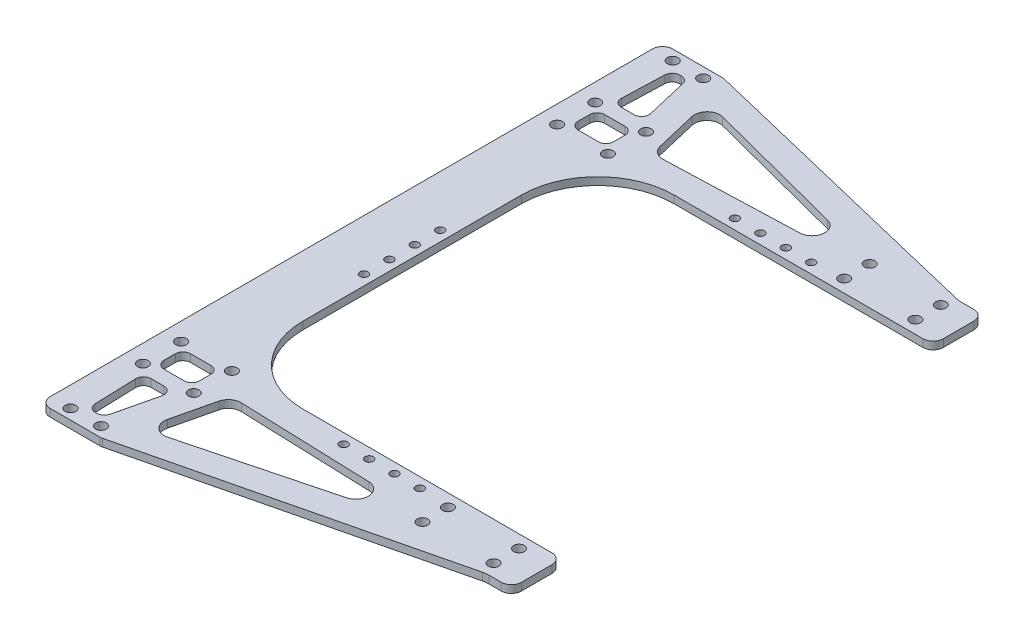
SolidWorks part; units mm, degrees
material "Thornel Mat VMA"
ref_plane "前视基准面" through (0, 0, 0) normal (0, 0, 1) x (1, 0, 0)
ref_plane "上视基准面" through (0, 0, 0) normal (0, 1, 0) x (1, 0, 0)
ref_plane "右视基准面" through (0, 0, 0) normal (1, 0, 0) x (0, 0, -1)
sketch "草图1" plane through (0, 0, 0) normal (0, 1, 0) x (1, 0, 0)
  line L0 (0, -83) -> (0, 83) construction
  line L5 (0, 0) -> (71.3718, 0) construction
  line L6 (14, 88) -> (-14, 88) construction
  line L7 (14, 88) -> (14, 78) construction
  line L8 (14, 78) -> (-14, 78) construction
  line L9 (-14, 88) -> (-14, 78) construction
  line L10 (14, 88) -> (-14, 78) construction
  line L11 (14, 78) -> (-14, 88) construction
  line L12 (14, -88) -> (-14, -88) construction
  line L13 (14, -88) -> (14, -78) construction
  line L14 (14, -78) -> (-14, -78) construction
  line L15 (-14, -88) -> (-14, -78) construction
  line L16 (14, -88) -> (-14, -78) construction
  line L17 (14, -78) -> (-14, -88) construction
  line L18 (-26, 93) -> (-96, 93)
  line L19 (26, 93) -> (-26, 93)
  line L20 (26, 93) -> (26, 73)
  line L21 (26, 73) -> (-26, 73) construction
  line L22 (-26, 93) -> (-26, 73) construction
  line L23 (26, 93) -> (-26, 73) construction
  line L24 (26, 73) -> (-26, 93) construction
  line L25 (-106, 103) -> (-106, 122.5)
  line L26 (-106, 122.5) -> (-130, 122.5)
  line L27 (-26, 73) -> (-76, 73) construction
  line L28 (-106, 43) -> (-106, -43)
  line L29 (26, -93) -> (26, -73)
  line L30 (26, -73) -> (-26, -73) construction
  line L31 (26, -93) -> (-26, -93)
  line L32 (-26, -93) -> (-96, -93)
  line L33 (-26, -73) -> (-76, -73) construction
  line L34 (-106, -103) -> (-106, -122.5)
  line L35 (-106, -122.5) -> (-130, -122.5)
  line L36 (-130, 122.5) -> (-130, -122.5)
  line L37 (-76, -73) -> (26, -73)
  line L38 (-76, 73) -> (26, 73)
  circle A0 centre (-14, 88) radius 2.1
  circle A1 centre (-14, 78) radius 2.1
  circle A4 centre (14, 78) radius 2.1
  circle A5 centre (14, 88) radius 2.1
  arc A6 (-96, 93) -> (-106, 103) centre (-96, 103) cw
  arc A7 (-76, 73) -> (-106, 43) centre (-76, 43) ccw
  circle A8 centre (14, -78) radius 2.1
  circle A9 centre (14, -88) radius 2.1
  circle A12 centre (-14, -78) radius 2.1
  circle A13 centre (-14, -88) radius 2.1
  arc A14 (-76, -73) -> (-106, -43) centre (-76, -43) cw
  arc A15 (-96, -93) -> (-106, -103) centre (-96, -103) ccw
  point P3 (0, 0)
  dimension "D4" = 4.2
  dimension "D8" = 10
  dimension "D11" = 30
  dimension "D1" = 166
  dimension "D2" = 10
  dimension "D3" = 28
  dimension "D5" = 20
  dimension "D6" = 52
  dimension "D7" = 106
  dimension "D9" = 24
  dimension "D10" = 245
extrude "凸台-拉伸1" add sketch "草图1" along normal blind 3
fillet "圆角1" radius 4 4 edges at (-130, 1.5, 122.5) (-130, 1.5, -122.5) (26, 1.5, 73) (26, 1.5, -73)
sketch "草图2" plane through (0, 3, 0) normal (0, 1, 0) x (1, 0, 0)
  line L0 (-116, 122.5) -> (-116, -122.5) construction
  line L1 (-106, 122.5) -> (-126, 122.5) construction
  line L2 (-126, -122.5) -> (-106, -122.5) construction
  line L4 (-110, -118.5) -> (-122, -118.5) construction
  line L5 (-110, -118.5) -> (-110, 118.5) construction
  line L6 (-110, 118.5) -> (-122, 118.5) construction
  line L7 (-122, -118.5) -> (-122, 118.5) construction
  line L8 (-110, -118.5) -> (-122, 118.5) construction
  line L9 (-110, 118.5) -> (-122, -118.5) construction
  circle A0 centre (-122, 118.5) radius 2.1
  circle A1 centre (-110, 118.5) radius 2.1
  circle A2 centre (-122, -118.5) radius 2.1
  circle A3 centre (-110, -118.5) radius 2.1
  point P6 (-116, 0)
  dimension "D3" = 4.2
  dimension "D1" = 12
  dimension "D2" = 4
extrude "切除-拉伸1" cut sketch "草图2" against normal through all
sketch "草图4" plane through (0, 3, 0) normal (0, 1, 0) x (1, 0, 0)
  line L0 (-106, 122.5) -> (16, 93)
  line L2 (16, 93) -> (-106, 93)
  line L3 (-106, 93) -> (-106, 122.5)
  line L5 (0, 0) -> (-106, 0) construction
  line L6 (-106, -43) -> (-106, 43) construction
  line L7 (16, -93) -> (-106, -93)
  line L8 (-106, -122.5) -> (16, -93)
  line L9 (-106, -93) -> (-106, -122.5)
  line L11 (26, 93) -> (-96, 93) construction
  line L12 (26, 77) -> (26, 93) construction
  dimension "D1" = 10
extrude "凸台-拉伸2" add sketch "草图4" against normal up to surface (3 mm away) up to face at (-110, 0, -116.4)
fillet "圆角2" radius 4 4 edges at (-106, 1.5, 122.5) (-106, 1.5, -122.5) (26, 1.5, 93) (26, 1.5, -93)
sketch "草图5" plane through (0, 0, 0) normal (0, -1, 0) x (1, 0, 0)
  line L0 (-130, 0) -> (115.8212, 0) construction
  line L1 (-130, -118.5) -> (-130, 118.5) construction
  line L2 (-110, 98.3119) -> (-110, -42.0796) construction
  line L4 (-106, 43) -> (-106, -43) construction
  line L5 (-20.7358, -77) -> (-173.6293, -77) construction
  line L6 (-76, -73) -> (22, -73) construction
  line L7 (-20.7358, 77) -> (-173.6293, 77) construction
  line L8 (-26, -77) -> (-36, -77) construction
  circle A0 centre (-110, -15) radius 1.6
  circle A1 centre (-110, -5) radius 1.6
  circle A2 centre (-110, 5) radius 1.6
  circle A3 centre (-110, 15) radius 1.6
  circle A4 centre (-110, -15) radius 2.84 construction
  circle A5 centre (-26, -77) radius 1.6
  circle A6 centre (-36, -77) radius 1.6
  circle A7 centre (-46, -77) radius 1.6
  circle A8 centre (-56, -77) radius 1.6
  circle A9 centre (-26, -77) radius 2.84 construction
  circle A10 centre (-14, -78) radius 3.61 construction
  circle A11 centre (-56, 77) radius 1.6
  circle A12 centre (-46, 77) radius 1.6
  circle A13 centre (-36, 77) radius 1.6
  circle A14 centre (-26, 77) radius 1.6
  dimension "D1" = 3.2
  dimension "D4" = 5.68
  dimension "D9" = 7.22
  dimension "D10" = 5.68
  dimension "D2" = 10
  dimension "D3" = 5
  dimension "D5" = 4
  dimension "D7" = 10
  dimension "D8" = 4
  dimension "D11" = 12
  dimension "D6" = 4
extrude "切除-拉伸2" cut sketch "草图5" against normal through all
fillet "圆角3" radius 10 2 edges at (16, 1.5, 93) (16, 1.5, -93)
sketch "草图6" plane through (0, 3, 0) normal (0, 1, 0) x (1, 0, 0)
  circle A0 centre (-110, 118.5) radius 2.1 construction
  circle A1 centre (-122, 118.5) radius 2.1 construction
  circle A2 centre (-110, -118.5) radius 2.1 construction
  circle A3 centre (-122, -118.5) radius 2.1 construction
  circle A4 centre (-110, 118.5) radius 2.1
  circle A5 centre (-122, 118.5) radius 2.1
  circle A6 centre (-110, -118.5) radius 2.1
  circle A7 centre (-122, -118.5) radius 2.1
extrude "凸台-拉伸3" [suppressed] add sketch "草图6" against normal up to surface (3 mm away)
sketch "草图7" plane through (0, 3, 0) normal (0, 1, 0) x (1, 0, 0)
  line L0 (-130, 0) -> (-50130, 0) construction
  line L1 (-130, 118.5) -> (-130, -118.5) construction
  line L3 (-123, -74) -> (-103, -74) construction
  line L4 (-123, -74) -> (-123, -89) construction
  line L5 (-123, -89) -> (-103, -89) construction
  line L6 (-103, -74) -> (-103, -89) construction
  line L7 (-113, -89) -> (-113, -74) construction
  line L8 (-123, -81.5) -> (-103, -81.5) construction
  line L9 (-130, 118.5) -> (-130, -118.5) construction
  line L10 (-123, 81.5) -> (-103, 81.5) construction
  line L11 (-113, 89) -> (-113, 74) construction
  line L12 (-103, 74) -> (-103, 89) construction
  line L13 (-123, 89) -> (-103, 89) construction
  line L14 (-123, 74) -> (-123, 89) construction
  line L15 (-123, 74) -> (-103, 74) construction
  line L16 (-126, -122.5) -> (-106.4767, -122.5) construction
  line L17 (-14, -78) -> (14, -78) construction
  line L18 (-14, -78) -> (-14, -88) construction
  line L19 (-14, -88) -> (14, -88) construction
  line L20 (14, -78) -> (14, -88) construction
  line L21 (0, -88) -> (0, -78) construction
  line L22 (-14, -83) -> (14, -83) construction
  circle A0 centre (-123, -74) radius 2.1
  circle A1 centre (-103, -74) radius 2.1
  circle A3 centre (-103, -89) radius 2.1
  circle A4 centre (-123, -89) radius 2.1
  circle A5 centre (-123, 89) radius 2.1
  circle A6 centre (-103, 89) radius 2.1
  circle A7 centre (-103, 74) radius 2.1
  circle A8 centre (-123, 74) radius 2.1
  point P4 (-130, 0)
  point P5 (-113, -81.5)
  point P29 (-113, 81.5)
  point P108 (0, -83)
  dimension "D3" = 4.2
  dimension "D1" = 20
  dimension "D2" = 15
  dimension "D4" = 41
  dimension "D5" = 17
extrude "切除-拉伸3" cut sketch "草图7" against normal through all
sketch "草图8" plane through (0, 3, 0) normal (0, 1, 0) x (1, 0, 0)
  line L0 (0, 0) -> (-197.4028, 0) construction
  line L9 (26, 77) -> (26, 89) construction
  line L10 (-99.1731, 103.1913) -> (-95.2909, 86.8306)
  line L15 (-118, 62.5) -> (-121, 62.5) construction
  line L16 (-124, 59.5) -> (-124, -59.5) construction
  line L17 (-121, -62.5) -> (-118, -62.5) construction
  line L18 (-115, -59.5) -> (-115, 59.5) construction
  line L19 (-130, 118.5) -> (-130, -118.5) construction
  line L23 (-103, 89) -> (-123, 89) construction
  line L24 (-123, 89) -> (-123, 74) construction
  line L25 (-123, 74) -> (-103, 74) construction
  line L26 (-103, 74) -> (-103, 89) construction
  line L27 (-103, 89) -> (-123, 74) construction
  line L28 (-109, 86.75) -> (-117, 86.75)
  line L29 (-106, 83.75) -> (-106, 79.25)
  line L30 (-109, 76.25) -> (-117, 76.25)
  line L31 (-120, 83.75) -> (-120, 79.25)
  line L32 (-103, 74) -> (-123, 89) construction
  line L33 (-109, -76.25) -> (-117, -76.25)
  line L34 (-120, -83.75) -> (-120, -79.25)
  line L35 (-109, -86.75) -> (-117, -86.75)
  line L36 (-106, -83.75) -> (-106, -79.25)
  line L37 (-110, 118.5) -> (-103, 89) construction
  line L38 (-110, 118.5) -> (-122, 118.5) construction
  line L39 (-122, 118.5) -> (-123, 89) construction
  line L44 (-115.1381, 115) -> (-115.7166, 115)
  line L45 (-118.7149, 112.1016) -> (-119.2742, 95.6016)
  line L46 (-111.2229, 92.5) -> (-116.2759, 92.5)
  line L47 (-112.2192, 112.6926) -> (-108.3039, 96.1926)
  line L48 (-107.4277, 92.5) -> (-119.3793, 92.5) construction
  line L49 (-112.7667, 115) -> (-107.4277, 92.5) construction
  line L50 (-118.6166, 115) -> (-119.3793, 92.5) construction
  line L51 (-112.7667, 115) -> (-118.6166, 115) construction
  line L52 (-37.1814, 94.639) -> (-93.0484, 109.1844)
  line L53 (-38.2667, 84.8034) -> (-90.2514, 82.988)
  line L54 (-4, 86) -> (-66.1315, 86) construction
  line L55 (-4, 86) -> (-51.4736, 97.4793) construction
  line L56 (14.8415, 93.2801) -> (-105.5366, 122.388) construction
  line L57 (-76, 73) -> (22, 73) construction
  line L58 (-37.1814, -94.639) -> (-93.0484, -109.1844)
  line L59 (-38.2667, -84.8034) -> (-90.2514, -82.988)
  line L60 (-99.1731, -103.1913) -> (-95.2909, -86.8306)
  line L61 (-112.2192, -112.6926) -> (-108.3039, -96.1926)
  line L62 (-111.2229, -92.5) -> (-116.2759, -92.5)
  line L63 (-118.7149, -112.1016) -> (-119.2742, -95.6016)
  line L64 (-115.1381, -115) -> (-115.7166, -115)
  arc A0 (-37.1814, 94.639) -> (-38.2667, 84.8034) centre (-38.4412, 89.8003) cw
  arc A10 (-118, -62.5) -> (-115, -59.5) centre (-118, -59.5) ccw construction
  arc A11 (-124, -59.5) -> (-121, -62.5) centre (-121, -59.5) ccw construction
  arc A12 (-121, 62.5) -> (-124, 59.5) centre (-121, 59.5) ccw construction
  arc A13 (-118, 62.5) -> (-115, 59.5) centre (-118, 59.5) cw construction
  arc A17 (-106, 83.75) -> (-109, 86.75) centre (-109, 83.75) ccw
  arc A18 (-117, 76.25) -> (-120, 79.25) centre (-117, 79.25) cw
  arc A19 (-117, 86.75) -> (-120, 83.75) centre (-117, 83.75) ccw
  arc A20 (-106, 79.25) -> (-109, 76.25) centre (-109, 79.25) cw
  arc A21 (-117, -76.25) -> (-120, -79.25) centre (-117, -79.25) ccw
  arc A22 (-117, -86.75) -> (-120, -83.75) centre (-117, -83.75) cw
  arc A23 (-106, -83.75) -> (-109, -86.75) centre (-109, -83.75) cw
  arc A24 (-106, -79.25) -> (-109, -76.25) centre (-109, -79.25) ccw
  arc A25 (-111.2229, 92.5) -> (-108.3039, 96.1926) centre (-111.2229, 95.5) ccw
  arc A26 (-119.2742, 95.6016) -> (-116.2759, 92.5) centre (-116.2759, 95.5) ccw
  arc A27 (-115.7166, 115) -> (-118.7149, 112.1016) centre (-115.7166, 112) ccw
  arc A28 (-115.1381, 115) -> (-112.2192, 112.6926) centre (-115.1381, 112) cw
  arc A29 (-90.2514, 82.988) -> (-95.2909, 86.8306) centre (-90.4259, 87.985) cw
  arc A30 (-93.0484, 109.1844) -> (-99.1731, 103.1913) centre (-94.3081, 104.3457) ccw
  arc A31 (-37.1814, -94.639) -> (-38.2667, -84.8034) centre (-38.4412, -89.8003) ccw
  arc A32 (-90.2514, -82.988) -> (-95.2909, -86.8306) centre (-90.4259, -87.985) ccw
  arc A33 (-93.0484, -109.1844) -> (-99.1731, -103.1913) centre (-94.3081, -104.3457) cw
  arc A34 (-111.2229, -92.5) -> (-108.3039, -96.1926) centre (-111.2229, -95.5) cw
  arc A35 (-119.2742, -95.6016) -> (-116.2759, -92.5) centre (-116.2759, -95.5) cw
  arc A36 (-115.7166, -115) -> (-118.7149, -112.1016) centre (-115.7166, -112) cw
  arc A37 (-115.1381, -115) -> (-112.2192, -112.6926) centre (-115.1381, -112) ccw
  point P25 (-4, 86)
  point P27 (-4, 86)
  point P47 (-124, -62.5)
  point P50 (-124, 62.5)
  point P53 (-115, 62.5)
  point P64 (-106, 86.75)
  point P67 (-120, 76.25)
  point P70 (-120, 86.75)
  dimension "D5" = 30
  dimension "D8" = 3
  dimension "D4" = 13
  dimension "D11" = 3
  dimension "D13" = 3
  dimension "D15" = 5
  dimension "D2" = 1
  dimension "D3" = 2
  dimension "D6" = 9
  dimension "D7" = 125
  dimension "D9" = 6
  dimension "D10" = 14
  dimension "D12" = 3.5
  dimension "D14" = 7
extrude "切除-拉伸4" cut sketch "草图8" against normal through all
